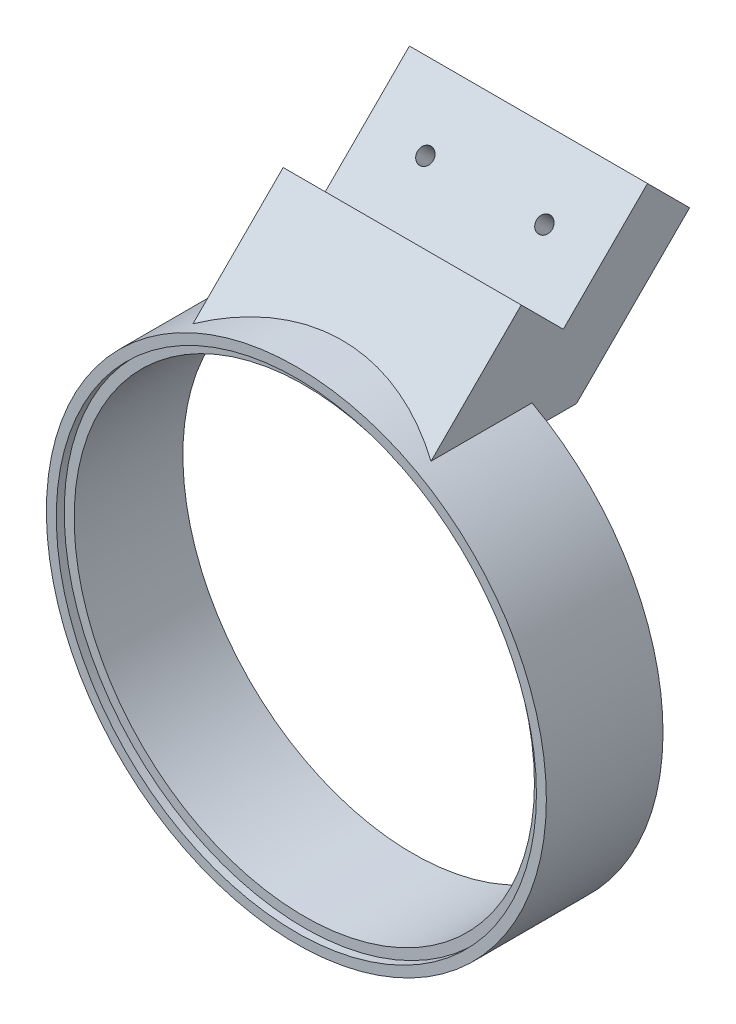
SolidWorks part; units mm, degrees
material "ABS"
ref_plane "Front Plane" through (0, 0, 0) normal (0, 0, 1) x (1, 0, 0)
ref_plane "Top Plane" through (0, 0, 0) normal (0, 1, 0) x (1, 0, 0)
ref_plane "Right Plane" through (0, 0, 0) normal (1, 0, 0) x (0, 0, -1)
sketch "Sketch1" plane through (0, 0, 0) normal (0, 0, 1) x (1, 0, 0)
  circle A0 centre (0, 0) radius 58
  circle A1 centre (0, 0) radius 63
  dimension "D1" = 116
  dimension "D2" = 5
extrude "Boss-Extrude1" add sketch "Sketch1" along normal blind 29.4
sketch "Sketch2" plane through (0, 0, 29.4) normal (0, 0, 1) x (1, 0, 0)
  circle A0 centre (0, 0) radius 58
  circle A1 centre (0, 0) radius 60.5
  circle A2 centre (0, 0) radius 58 construction
  dimension "D1" = 2.5
extrude "Cut-Extrude1" cut sketch "Sketch2" against normal blind 2
sketch "Sketch3" plane through (0, 0, 0) normal (0, 1, 0) x (1, 0, 0)
  line L0 (63, 0) -> (-63, 0) construction
  line L1 (-30, -29.4) -> (30, -29.4)
  line L2 (-30, -29.4) -> (-30, 0)
  line L3 (-30, 0) -> (30, 0)
  line L4 (30, -29.4) -> (30, 0)
  line L5 (-30, -29.4) -> (30, 0) construction
  line L6 (-30, 0) -> (30, -29.4) construction
  point P0 (0, -14.7)
  dimension "D1" = 29.4
  dimension "D2" = 60
extrude "Boss-Extrude2" add sketch "Sketch3" along normal blind 20 from surface starting at face at (63, 0, 29.4)
sketch "Sketch5" plane through (-30, 0, 0) normal (-1, 0, 0) x (0, 0, 1)
  line L0 (0, 75.3986) -> (0, 99.8623)
  line L1 (0, 99.8623) -> (29.4, 99.8623)
  line L2 (29.4, 99.8623) -> (29.4, 75.3986)
  line L3 (29.4, 75.3986) -> (0, 75.3986)
extrude "Cut-Extrude2" cut sketch "Sketch5" against normal up to surface (60 mm away) up to face at (30, 65.3986, 14.7)
sketch "Sketch6" plane through (-30, 0, 0) normal (-1, 0, 0) x (0, 0, 1)
  line L3 (0, 75.3986) -> (29.4, 104.7986)
  line L4 (29.4, 104.7986) -> (29.4, 75.3986)
  line L5 (29.4, 75.3986) -> (0, 75.3986)
  dimension "D1" = 45
extrude "Boss-Extrude3" add sketch "Sketch6" against normal up to surface (60 mm away) up to face at (30, 65.3986, 14.7)
sketch "Sketch7" plane through (0, 37.6993, -37.6993) normal (0, 0.7071, -0.7071) x (1, 0, 0)
  line L4 (-30, -94.8927) -> (30, -94.8927)
  line L5 (30, -94.8927) -> (30, -53.3148)
  line L6 (30, -53.3148) -> (-30, -53.3148)
  line L7 (-30, -53.3148) -> (-30, -94.8927)
  line L8 (-30, -94.8927) -> (30, -94.8927)
  line L9 (30, -94.8927) -> (30, -53.3148)
  line L10 (30, -53.3148) -> (-30, -53.3148)
  line L11 (-30, -53.3148) -> (-30, -94.8927)
  dimension "D1" = 0
extrude "Boss-Extrude4" add sketch "Sketch7" along normal blind 50
sketch "Sketch8" plane through (30, 0, 0) normal (1, 0, 0) x (0, 0, -1)
  line L0 (14.5664, 131.5428) -> (-29.4, 87.5764)
  line L1 (5.9553, 140.1539) -> (35.3553, 110.7539) construction
  line L2 (-29.4, 55.3986) -> (-29.4, 104.7986) construction
  line L3 (-29.4, 87.5764) -> (-29.4, 104.7986)
  line L4 (-29.4, 104.7986) -> (5.9553, 140.1539)
  line L5 (5.9553, 140.1539) -> (14.5664, 131.5428)
  line L6 (35.3553, 110.7539) -> (0, 75.3986) construction
  dimension "D1" = 29.4
extrude "Cut-Extrude3" cut sketch "Sketch8" against normal up to next
sketch "Sketch9" plane through (0, 37.6993, 37.6993) normal (0, -0.7071, -0.7071) x (1, 0, 0)
  line L4 (30, -53.3148) -> (-30, -53.3148)
  line L5 (-30, -53.3148) -> (-30, -103.3148)
  line L6 (-30, -103.3148) -> (30, -103.3148)
  line L7 (30, -103.3148) -> (30, -53.3148)
  line L8 (30, -53.3148) -> (-30, -53.3148)
  line L9 (-30, -53.3148) -> (-30, -103.3148)
  line L10 (-30, -103.3148) -> (30, -103.3148)
  line L11 (30, -103.3148) -> (30, -53.3148)
  dimension "D1" = 0
extrude "Boss-Extrude5" add sketch "Sketch9" along normal blind 26.14
sketch "Sketch10" plane through (0, 37.6993, -37.6993) normal (0, -0.7071, 0.7071) x (1, 0, 0)
  line L4 (30, 53.3148) -> (-30, 53.3148)
  line L5 (-30, 53.3148) -> (-30, 27.1748)
  line L6 (-30, 27.1748) -> (30, 27.1748)
  line L7 (30, 27.1748) -> (30, 53.3148)
  line L8 (30, 53.3148) -> (-30, 53.3148)
  line L9 (-30, 53.3148) -> (-30, 27.1748)
  line L10 (-30, 27.1748) -> (30, 27.1748)
  line L11 (30, 27.1748) -> (30, 53.3148)
  dimension "D1" = 0
extrude "Boss-Extrude6" add sketch "Sketch10" along normal blind 30
sketch "Sketch11" plane through (0, 0, 29.4) normal (0, 0, 1) x (1, 0, 0)
  circle A0 centre (0, 0) radius 58
  circle A1 centre (0, 0) radius 58 construction
extrude "Cut-Extrude4" cut sketch "Sketch11" against normal through all
sketch "Sketch14" plane through (0, 0, 29.4) normal (0, 0, 1) x (1, 0, 0)
  line L0 (-30, 55.3986) -> (-30, 142.9473)
  line L1 (-30, 142.9473) -> (30, 142.9473)
  line L2 (30, 142.9473) -> (30, 55.3986)
  line L3 (30, 55.3986) -> (30, 142.9473)
  arc A0 (30, 55.3986) -> (-30, 55.3986) centre (0, 0) ccw
  line M1 (30, 87.5764) -> (-30, 87.5764)
  line M2 (-30, 87.5764) -> (-30, 55.3986)
  line M4 (30, 55.3986) -> (30, 87.5764)
extrude "Cut-Extrude5" cut sketch "Sketch14" against normal blind 14.7 contours L2 L1 L0 M1 | A0 M4 M1 M2
sketch "Sketch15" plane through (30, 0, 0) normal (1, 0, 0) x (0, 0, -1)
  line L0 (32.6259, 113.4833) -> (-14.7, 66.1574)
  line L1 (14.5664, 131.5428) -> (53.8391, 92.2701) construction
  line L2 (-14.7, 102.2764) -> (-14.7, 55.3986) construction
  line L3 (-14.7, 66.1574) -> (-14.7, 102.2764)
  line L4 (-14.7, 102.2764) -> (14.5664, 131.5428)
  line L5 (14.5664, 131.5428) -> (32.6259, 113.4833)
  line L6 (53.8391, 92.2701) -> (11.2077, 49.6387) construction
  dimension "D1" = 30
extrude "Cut-Extrude6" cut sketch "Sketch15" against normal up to next
sketch "Sketch16" plane through (30, 0, 0) normal (1, 0, 0) x (0, 0, -1)
  line L0 (-14.7, 66.1574) -> (-25.4589, 55.3986)
  line L1 (-25.4589, 55.3986) -> (-14.7, 55.3986)
  line L2 (-14.7, 55.3986) -> (-14.7, 66.1574)
extrude "Boss-Extrude7" add sketch "Sketch16" against normal up to surface (60 mm away) up to face at (-30, 68.8551, -9.7532)
sketch "Sketch17" plane through (0, 0, 29.4) normal (0, 0, 1) x (1, 0, 0)
  circle A0 centre (0, 0) radius 58
  circle A1 centre (0, 0) radius 58 construction
extrude "Cut-Extrude7" cut sketch "Sketch17" against normal through all
sketch "Sketch18" plane through (0, 73.0546, -73.0546) normal (0, 0.7071, -0.7071) x (1, 0, 0)
  line L1 (-30, -57.1748) -> (30, -57.1748)
  line L2 (-30, -57.1748) -> (-30, -42.1748)
  line L3 (-30, -42.1748) -> (30, -42.1748)
  line L4 (30, -57.1748) -> (30, -42.1748)
  line L5 (-30, -27.1748) -> (30, -27.1748) construction
  dimension "D1" = 15
extrude "Cut-Extrude8" cut sketch "Sketch18" against normal blind 50
sketch "Sketch19" plane through (0, 19.2155, 19.2155) normal (0, -0.7071, -0.7071) x (1, 0, 0)
  circle A2 centre (15, -67.7888) radius 2
  circle A3 centre (-15, -67.7888) radius 2
  dimension "D1" = 4
  dimension "D2" = 4
extrude "Cut-Extrude9" cut sketch "Sketch19" against normal up to surface (15 mm away) up to face at (0, 85.1991, -25.5548)
sketch "Sketch20" plane through (0, 29.8221, 29.8221) normal (0, 0.7071, 0.7071) x (1, 0, 0)
  line L0 (30, 53.3148) -> (30, 103.3148) construction
  line L1 (-30, 103.3148) -> (30, 103.3148)
  line L2 (-30, 103.3148) -> (-30, 83.3148)
  line L3 (-30, 83.3148) -> (30, 83.3148)
  line L4 (30, 103.3148) -> (30, 83.3148)
  dimension "D1" = 20
extrude "Cut-Extrude10" cut sketch "Sketch20" against normal through all
